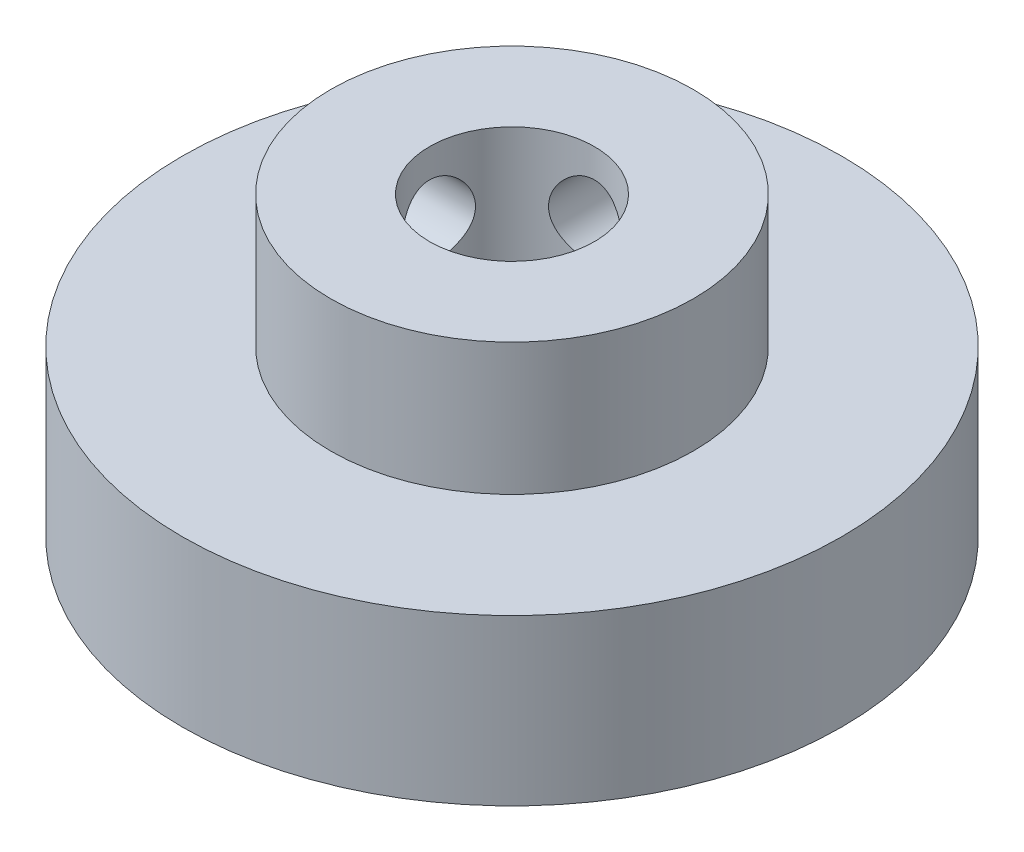
SolidWorks part; units mm, degrees
ref_plane "Front Plane" through (0, 0, 0) normal (0, 0, 1) x (1, 0, 0)
ref_plane "Top Plane" through (0, 0, 0) normal (0, 1, 0) x (1, 0, 0)
ref_plane "Right Plane" through (0, 0, 0) normal (1, 0, 0) x (0, 0, -1)
sketch "Sketch1" plane through (0, 0, 0) normal (0, 1, 0) x (1, 0, 0)
  circle A0 centre (0, 0) radius 11
  dimension "D1" = 22
extrude "Boss-Extrude1" add sketch "Sketch1" along normal blind 18
sketch "Sketch2" plane through (0, 0, 0) normal (0, -1, 0) x (1, 0, 0)
  circle A0 centre (0, 0) radius 20
  dimension "D1" = 40
extrude "Boss-Extrude2" add sketch "Sketch2" against normal blind 10
sketch "Sketch3" plane through (0, 18, 0) normal (0, 1, 0) x (1, 0, 0)
  circle A0 centre (0, 0) radius 5
  dimension "D1" = 10
extrude "Cut-Extrude1" cut sketch "Sketch3" against normal through all both and the other way through all
sketch "Sketch4" plane through (0, 0, 0) normal (0, -1, 0) x (1, 0, 0)
  line L0 (0, 0) -> (-10.6066, 10.6066) construction
  line L1 (0, 0) -> (0, 20) construction
  circle A0 centre (-10.6066, 10.6066) radius 2.25
  circle A1 centre (0, 0) radius 20 construction
  dimension "D1" = 4.5
  dimension "D2" = 15
  dimension "D3" = 45
extrude "Cut-Extrude2" cut sketch "Sketch4" against normal blind 7
pattern_circular "CirPattern1" count 4 over 360 about axis through (0, 0, 0) along (0, 1, 0) of "Cut-Extrude2"
sketch "Sketch5" plane through (0, 0, 0) normal (0, 0, 1) x (1, 0, 0)
  line L0 (0, 18) -> (0, 0) construction
  line L1 (11, 18) -> (-11, 18) construction
  line L2 (-20, 0) -> (20, 0) construction
  circle A0 centre (0, 14) radius 2.25
  circle A1 centre (0, 5) radius 2.25
  dimension "D1" = 4.5
  dimension "D2" = 4
  dimension "D3" = 5
  dimension "D4" = 4.5
extrude "Cut-Extrude3" cut sketch "Sketch5" against normal through all
pattern_circular "CirPattern2" count 2 every 90 about axis through (0, 18, 0) along (0, 1, 0) of "Cut-Extrude3"
